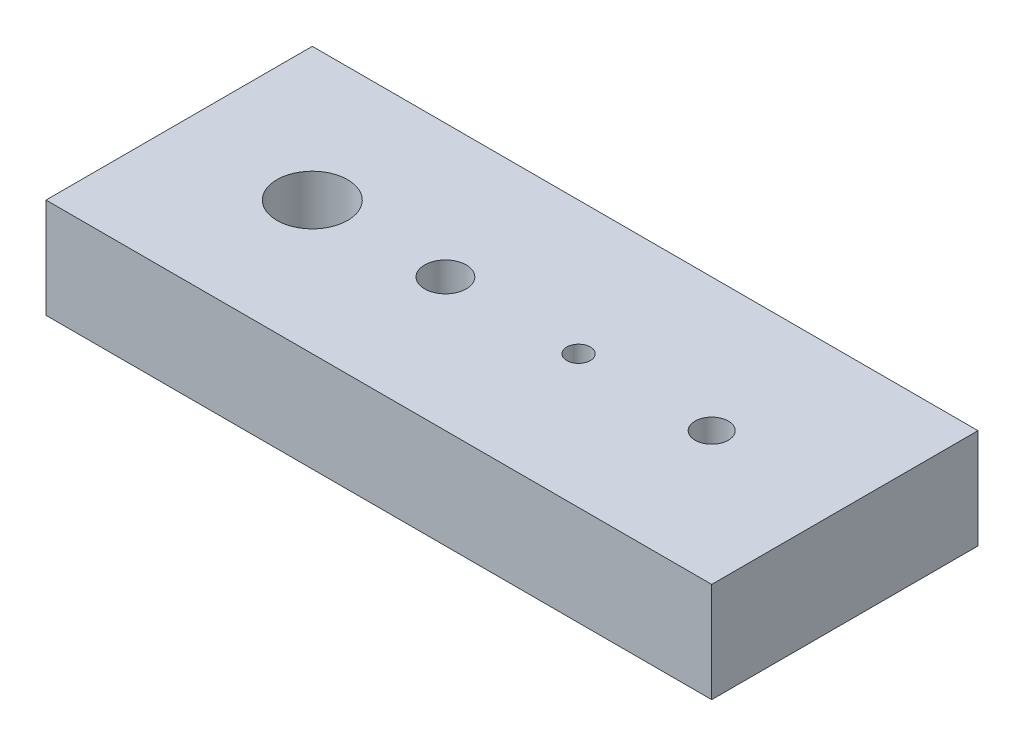
SolidWorks part; units mm, degrees
ref_plane "Front Plane" through (0, 0, 0) normal (0, 0, 1) x (1, 0, 0)
ref_plane "Top Plane" through (0, 0, 0) normal (0, 1, 0) x (1, 0, 0)
ref_plane "Right Plane" through (0, 0, 0) normal (1, 0, 0) x (0, 0, -1)
sketch "Sketch1" plane through (0, 0, 0) normal (0, 0, 1) x (1, 0, 0)
  line L1 (0, 0) -> (127, 0)
  line L2 (0, 0) -> (0, 19.05)
  line L3 (0, 19.05) -> (127, 19.05)
  line L4 (127, 0) -> (127, 19.05)
  dimension "D1" = 19.05
  dimension "D2" = 127
extrude "Boss-Extrude1" add sketch "Sketch1" along normal blind 50.8
sketch "Sketch2" plane through (0, 19.05, 0) normal (0, 1, 0) x (1, 0, 0)
  line L0 (0, -25.4) -> (127, -25.4) construction
  line L1 (0, -50.8) -> (0, 0) construction
  line L2 (127, -50.8) -> (127, 0) construction
  point P6 (25.4, -25.4)
  point P7 (50.8, -25.4)
  point P8 (76.2, -25.4)
  point P9 (101.6, -25.4)
  dimension "D1" = 25.4
  dimension "D2" = 50.8
  dimension "D3" = 76.2
  dimension "D4" = 101.6
hole_wizard "1/2 Clearance Hole1" positions "Sketch3" profile "Sketch4" hole size "1/2" standard "ANSI Inch" end condition through all
sketch "Sketch3" plane through (0, 19.05, 0) normal (0, 1, 0) x (1, 0, 0)
  point P0 (25.4, -25.4)
sketch "Sketch4" plane through (25.4, 19.05, 25.4) normal (1, 0, 0) x (0, 0, 1)
  line L0 (0, 0) -> (0, 19.05)
  line L1 (0, 19.05) -> (6.7462, 19.05)
  line L2 (6.7462, 19.05) -> (6.7462, 0)
  line L5 (6.7462, 0) -> (0, 0)
  line L11 (0, -6.35) -> (0, 107.95) construction
  dimension "Thru Hole Dia." = 13.4925
  dimension "Thru Hole Depth" = 19.05
hole_wizard "3/8-16 Tapped Hole1" positions "Sketch5" profile "Sketch6" tap size "3/8-16" standard "ANSI Inch" end condition through all
sketch "Sketch5" plane through (0, 19.05, 0) normal (0, 1, 0) x (1, 0, 0)
  point P0 (50.8, -25.4)
cosmetic thread "Hole Thread1" parameters "D2"=9.525
sketch "Sketch6" plane through (50.8, 19.05, 25.4) normal (1, 0, 0) x (0, 0, 1)
  line L0 (0, 0) -> (0, 19.05)
  line L1 (0, 19.05) -> (3.9687, 19.05)
  line L2 (3.9687, 19.05) -> (3.9688, 0)
  line L5 (3.9688, 0) -> (0, 0)
  line L11 (0, -6.35) -> (0, 107.95) construction
  dimension "Thru Tap Drill Dia." = 7.9375
  dimension "Thru Tap Drill Depth" = 19.05
hole_wizard "#12-24 Tapped Hole1" positions "Sketch7" profile "Sketch8" tap size "#12-24" standard "ANSI Inch" end condition through all
sketch "Sketch7" plane through (0, 19.05, 0) normal (0, 1, 0) x (1, 0, 0)
  point P0 (76.2, -25.4)
sketch "Sketch8" plane through (76.2, 19.05, 25.4) normal (1, 0, 0) x (0, 0, 1)
  line L0 (0, 0) -> (0, 19.05)
  line L1 (0, 19.05) -> (2.2479, 19.05)
  line L2 (2.2479, 19.05) -> (2.2479, 0)
  line L5 (2.2479, 0) -> (0, 0)
  line L11 (0, -6.35) -> (0, 107.95) construction
  dimension "Thru Tap Drill Dia." = 4.4958
  dimension "Thru Tap Drill Depth" = 19.05
cosmetic thread "Hole Thread2" parameters "D2"=5.4864
hole_wizard "1/4 (0.25) Diameter Hole1" positions "Sketch11" profile "Sketch12" hole size "1/4" standard "ANSI Inch" end condition through all
sketch "Sketch11" plane through (0, 19.05, 0) normal (0, 1, 0) x (1, 0, 0)
  point P0 (101.6, -25.4)
sketch "Sketch12" plane through (101.6, 19.05, 25.4) normal (1, 0, 0) x (0, 0, 1)
  line L0 (0, 0) -> (0, 19.05)
  line L1 (0, 19.05) -> (3.175, 19.05)
  line L2 (3.175, 19.05) -> (3.175, 0)
  line L5 (3.175, 0) -> (0, 0)
  line L11 (0, -6.35) -> (0, 107.95) construction
  dimension "Thru Hole Dia." = 6.35
  dimension "Thru Hole Depth" = 19.05
